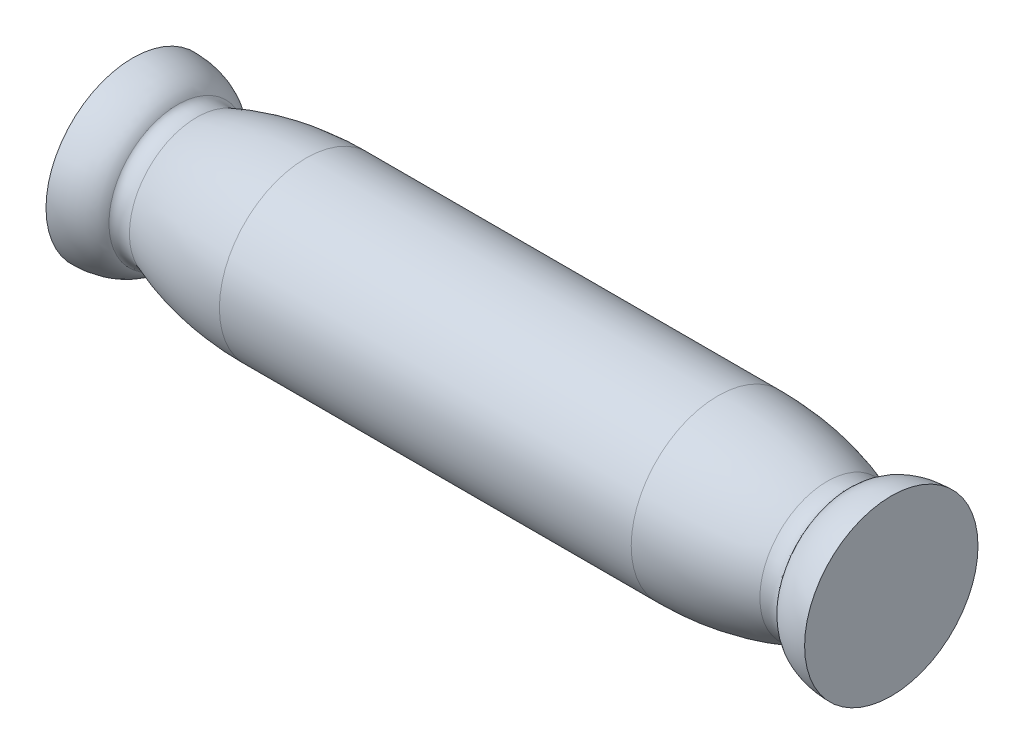
SolidWorks part; units mm, degrees
ref_plane "Front Plane" through (0, 0, 0) normal (0, 0, 1) x (1, 0, 0)
ref_plane "Top Plane" through (0, 0, 0) normal (0, 1, 0) x (1, 0, 0)
ref_plane "Right Plane" through (0, 0, 0) normal (1, 0, 0) x (0, 0, -1)
sketch "Sketch2" plane through (0, 0, 0) normal (1, 0, 0) x (0, 0, -1)
  circle A0 centre (0, 0) radius 4
  dimension "D1" = 8
extrude "Boss-Extrude1" add sketch "Sketch2" along normal blind 35
sketch "Sketch3" plane through (0, 0, 0) normal (-1, 0, 0) x (0, 0, 1)
  line L0 (-1.249, -1) -> (1.249, -1)
  line L1 (0, 0) -> (0, 5.7093) construction
  arc A0 (1.249, -1) -> (-1.249, -1) centre (0, 0) ccw
  point P6 (0, 1.6)
  dimension "D1" = 1.6
  dimension "D2" = 2.6
extrude "Cut-Extrude1" cut sketch "Sketch3" against normal blind 9.8
sketch "Sketch4" plane through (0, 0, 0) normal (0, 0, 1) x (1, 0, 0)
  line L0 (0, 4) -> (8, 4)
  line L1 (17.5, 7.5) -> (17.5, 1.6019) construction
  line L2 (27, 4) -> (35, 4)
  ellipse E0 centre (0, 2.8159) end of major axis (-2.1638, 2.8159) minor radius 1.1841 (2.0681, 3.1643) -> (0, 4) ccw
  ellipse E1 centre (3.1038, 4) end of major axis (2.0681, 3.1643) minor radius 0.6982 (2.0681, 3.1643) -> (2.9561, 3.1077) ccw
  ellipse E2 centre (8, -0.4167) end of major axis (-0.3688, -0.4167) minor radius 4.4167 (8, 4) -> (2.9561, 3.1077) ccw
  ellipse E3 centre (27, -0.4167) end of major axis (18.6312, -0.4167) minor radius 4.4167 (27, 4) -> (32.0439, 3.1077) cw
  ellipse E4 centre (31.8962, 4) end of major axis (30.8604, 4.8357) minor radius 0.6982 (32.9319, 3.1643) -> (32.0439, 3.1077) cw
  ellipse E5 centre (35, 2.8159) end of major axis (37.1638, 2.8159) minor radius 1.1841 (32.9319, 3.1643) -> (35, 4) cw
  dimension "D1" = 8
  dimension "D2" = 0.8357
  dimension "D3" = 2.0681
  dimension "D4" = 2.1638
  dimension "D5" = 2.6654
  dimension "D6" = 2.9561
  dimension "D7" = 3.1038
sketch "Sketch6" plane through (0, 0, 0) normal (0, 0, 1) x (1, 0, 0)
  line L0 (0, 0) -> (36.7329, 0) construction
revolve "Cut-Revolve1" cut sketch "Sketch4" angle 360 about L0
